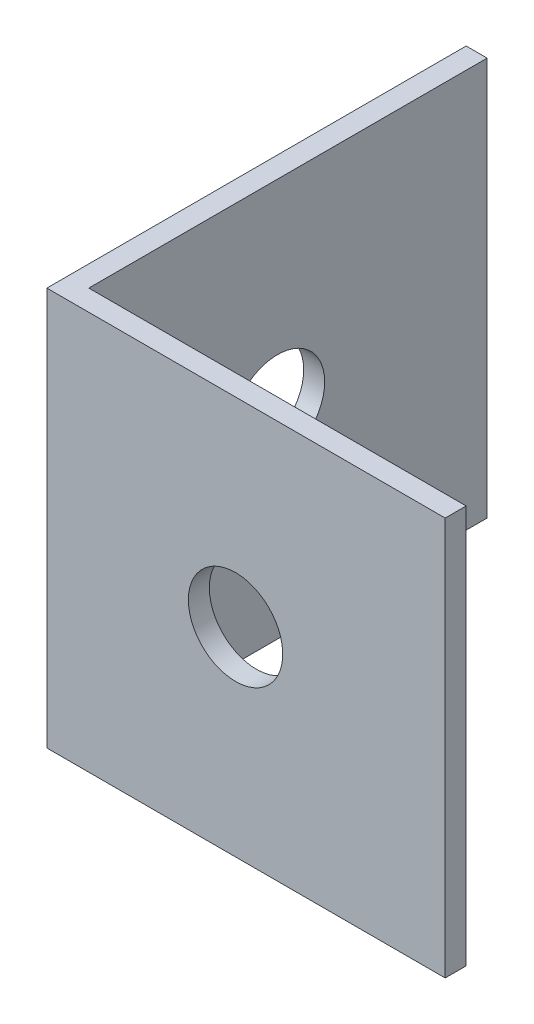
SolidWorks part; units mm, degrees
material "1060 Сплав"
ref_plane "Спереди" through (0, 0, 0) normal (0, 0, 1) x (1, 0, 0)
ref_plane "Сверху" through (0, 0, 0) normal (0, 1, 0) x (1, 0, 0)
ref_plane "Справа" through (0, 0, 0) normal (1, 0, 0) x (0, 0, -1)
sketch "Эскиз1" plane through (0, 0, 0) normal (0, 1, 0) x (1, 0, 0)
  line L0 (0, 0) -> (0, 20)
  line L1 (0, 20) -> (1, 20)
  line L2 (1, 20) -> (1, 1)
  line L3 (1, 1) -> (20, 1)
  line L4 (20, 1) -> (20, 0)
  line L5 (20, 0) -> (0, 0)
  dimension "D1" = 1
  dimension "D2" = 20
extrude "Бобышка-Вытянуть1" add sketch "Эскиз1" along normal blind 19
sketch "Эскиз2" plane through (20, 0, 0) normal (1, 0, 0) x (0, 0, -1)
  line L4 (0, 0) -> (1, 0)
  line L5 (1, 0) -> (1, 19)
  line L6 (1, 19) -> (0, 19)
  line L7 (0, 19) -> (0, 0)
  line L8 (0, 0) -> (1, 0)
  line L9 (1, 0) -> (1, 19)
  line L10 (1, 19) -> (0, 19)
  line L11 (0, 19) -> (0, 0)
  dimension "D1" = 0
extrude "Вырез-Вытянуть1" cut sketch "Эскиз2" against normal blind 1
sketch "Эскиз3" plane through (0, 0, -1) normal (0, 0, -1) x (-1, 0, 0)
  line L0 (-19, 9.5) -> (-9, 9.5) construction
  line L1 (-19, 0) -> (-19, 19) construction
  circle A0 centre (-9, 9.5) radius 2.25
  dimension "D2" = 4.5
  dimension "D1" = 10
extrude "Вырез-Вытянуть2" cut sketch "Эскиз3" against normal through all
sketch "Эскиз4" plane through (1, 0, 0) normal (1, 0, 0) x (0, 0, -1)
  line L0 (20, 9.5) -> (10, 9.5) construction
  line L1 (20, 19) -> (20, 0) construction
  circle A0 centre (10, 9.5) radius 2.25
  dimension "D1" = 10
  dimension "D2" = 4.5
extrude "Вырез-Вытянуть3" cut sketch "Эскиз4" against normal through all
